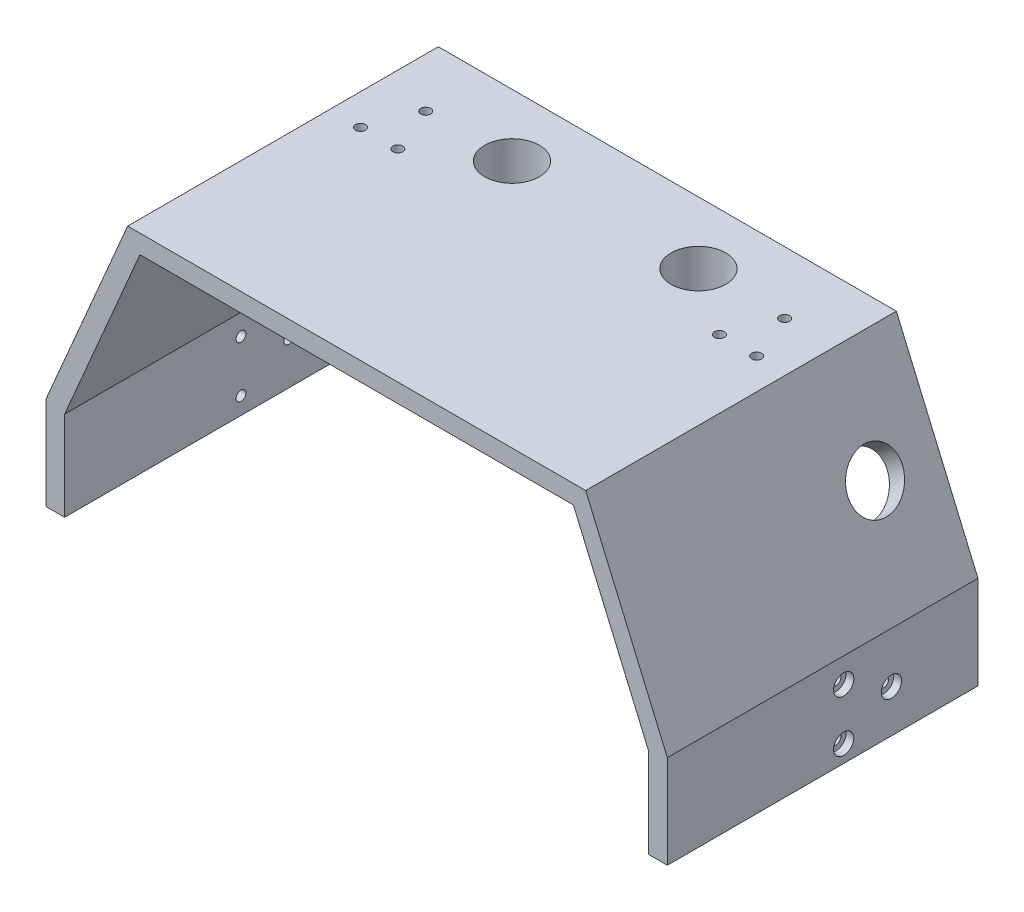
SolidWorks part; units mm, degrees
ref_plane "Alzado" through (0, 0, 0) normal (0, 0, 1) x (1, 0, 0)
ref_plane "Planta" through (0, 0, 0) normal (0, 1, 0) x (1, 0, 0)
ref_plane "Vista lateral" through (0, 0, 0) normal (1, 0, 0) x (0, 0, -1)
sketch "Croquis1" plane through (0, 0, 0) normal (0, 0, 1) x (1, 0, 0)
  line L1 (-100, 25) -> (-73.7179, 86.3249) construction
  line L2 (-73.7179, 86.3249) -> (73.7179, 86.3249) construction
  line L3 (100, 25) -> (100, -5) construction
  line L4 (100, 25) -> (73.7179, 86.3249) construction
  line L5 (-100, 25) -> (-100, -5)
  line L6 (-100, 25) -> (-73.7179, 86.3249)
  line L7 (-73.7179, 86.3249) -> (73.7179, 86.3249)
  line L8 (100, 25) -> (100, -5)
  line L9 (100, 25) -> (73.7179, 86.3249)
  line L10 (-94, 23.7685) -> (-94, -5)
  line L11 (-94, 23.7685) -> (-69.7615, 80.3249)
  line L12 (-69.7615, 80.3249) -> (69.7615, 80.3249)
  line L13 (94, 23.7685) -> (69.7615, 80.3249)
  line L14 (94, 23.7685) -> (94, -5)
  line L15 (-94, -5) -> (-100, -5)
  line L16 (100, -5) -> (94, -5)
  dimension "D2" = 30
  dimension "D1" = 6
extrude "Saliente-Extruir1" add sketch "Croquis1" along normal blind 100
sketch "Croquis3" plane through (0, 86.3249, 0) normal (0, 1, 0) x (1, 0, 0)
  line L0 (73.7179, 0) -> (-73.7179, 0) construction
  line L1 (73.7179, -100) -> (73.7179, 0) construction
  line L2 (-73.7179, -100) -> (-73.7179, 0) construction
  circle A2 centre (-30, -20) radius 8.8
  circle A3 centre (30, -20) radius 8.8
  dimension "D4" = 17.6
  dimension "D5" = 17.6
  dimension "D1" = 20
  dimension "D2" = 20
  dimension "D3" = 43.7179
  dimension "D6" = 43.7179
extrude "Cortar-Extruir1" cut sketch "Croquis3" against normal up to next
ref_plane "Plano1" through (-87.4795, 68.8361, 0) normal (-0.7859, 0.6184, 0) x (0, 0, -1)
sketch "Croquis4" plane through (-87.4795, 68.8361, 0) normal (-0.7859, 0.6184, 0) x (0, 0, -1)
  line L0 (0, -22.254) -> (0, 42.1921) construction
  line L1 (-100, -22.254) -> (0, -22.254) construction
  line L2 (-100, -22.254) -> (-100, 42.1921) construction
  line L3 (-100, 42.1921) -> (0, 42.1921) construction
  line L4 (0, -22.254) -> (0, 42.1921) construction
  line L5 (-100, -22.254) -> (0, -22.254) construction
  line L6 (-100, -22.254) -> (-100, 42.1921) construction
  line L7 (-100, 42.1921) -> (0, 42.1921) construction
  line L8 (0, 9.9691) -> (-100, 9.9691) construction
  circle A0 centre (-20, 9.9691) radius 8.8
  dimension "D1" = 17.6
  dimension "D2" = 20
extrude "Cortar-Extruir2" cut sketch "Croquis4" against normal up to next
mirror "Simetría1" about plane through (0, 0, 0) normal (1, 0, 0) of "Cortar-Extruir2"
sketch "Croquis5" plane through (0, 80.3249, 0) normal (0, -1, 0) x (1, 0, 0)
  line L0 (15.175, 0) -> (15.175, 2.3)
  line L1 (15.175, 2.3) -> (3.7842, 2.3)
  line L3 (-3.7842, 2.3) -> (-15.175, 2.3)
  line L4 (-15.175, 2.3) -> (-15.175, 0)
  line L10 (-14.875, 0) -> (-3.2619, 0)
  line L11 (3.2619, 0) -> (14.875, 0)
  line L12 (14.875, 0) -> (14.875, 2)
  line L13 (14.875, 2) -> (3.7202, 2)
  line L14 (-3.7202, 2) -> (-14.875, 2)
  line L15 (-14.875, 2) -> (-14.875, 0)
  line L17 (-15.175, 0) -> (3.2619, 0)
  line L19 (-3.2619, 0) -> (15.175, 0)
  line L20 (14.875, 0) -> (14.875, 2)
  line L22 (14.875, 2) -> (3.7202, 2)
  line L23 (-3.7202, 2) -> (-14.875, 2)
  line L24 (-14.875, 2) -> (-14.875, 0)
  arc A0 (3.7842, 2.3) -> (-3.7842, 2.3) centre (0, -6.25) ccw
  arc A3 (3.2619, 0) -> (-3.2619, 0) centre (0, -6.25) ccw
  arc A4 (3.7202, 2) -> (-3.7202, 2) centre (0, -6.25) ccw
  arc A5 (3.2619, 0) -> (-3.2619, 0) centre (0, -6.25) ccw
  arc A7 (3.7202, 2) -> (-3.7202, 2) centre (0, -6.25) ccw
  dimension "D1" = 0
  dimension "D2" = 0.3
extrude "Cortar-Extruir3" cut sketch "Croquis5" against normal blind 0.5
sketch "Croquis6" plane through (-100, 0, 0) normal (-1, 0, 0) x (0, 0, 1)
  circle A0 centre (43.227, 0.4977) radius 1.6 construction
  circle A1 centre (27.8635, 8.7685) radius 1.6 construction
  circle A2 centre (43.227, 17.0392) radius 1.6 construction
  circle A3 centre (43.227, 0.4977) radius 1.6
  circle A4 centre (27.8635, 8.7685) radius 1.6
  circle A5 centre (43.227, 17.0392) radius 1.6
extrude "Cortar-Extruir4" cut sketch "Croquis6" against normal up to next
sketch "Croquis7" plane through (-100, 0, 0) normal (-1, 0, 0) x (0, 0, 1)
  circle A0 centre (27.8635, 8.7685) radius 3.25
  circle A1 centre (43.227, 0.4977) radius 3.25
  circle A2 centre (43.227, 17.0392) radius 3.25
  dimension "D1" = 6.5
extrude "Cortar-Extruir5" cut sketch "Croquis7" against normal blind 2.5
mirror "Simetría2" about plane through (0, 0, 0) normal (1, 0, 0) of "Cortar-Extruir5", "Cortar-Extruir4"
sketch "Croquis11" plane through (0, 80.3249, 0) normal (0, -1, 0) x (1, 0, 0)
  circle A0 centre (30, 20) radius 8.8 construction
  circle A1 centre (-30, 20) radius 8.8 construction
  circle A2 centre (30, 20) radius 8.8
  circle A3 centre (-30, 20) radius 8.8
  circle A4 centre (-30, 20) radius 10.3
  circle A5 centre (30, 20) radius 10.3
  dimension "D1" = 1.5
extrude "Saliente-Extruir2" add sketch "Croquis11" along normal blind 10
ref_plane "Plano2" through (-63.9034, 50.2844, 0) normal (-0.7859, 0.6184, 0) x (0, 0, -1)
sketch "Croquis12" plane through (-63.9034, 50.2844, 0) normal (-0.7859, 0.6184, 0) x (0, 0, -1)
  circle A0 centre (-20, 9.9691) radius 8.8 construction
  circle A1 centre (-20, 9.9691) radius 8.8
  circle A2 centre (-20, 9.9691) radius 10.3
  dimension "D1" = 1.5
extrude "Saliente-Extruir3" add sketch "Croquis12" along normal up to next
sketch "Croquis13" plane through (0, 80.3249, 0) normal (0, -1, 0) x (1, 0, 0)
  circle A0 centre (57.7615, 20) radius 1.6 construction
  circle A1 centre (51.7615, 35) radius 1.6 construction
  circle A2 centre (63.7615, 35) radius 1.6 construction
  circle A3 centre (-57.7615, 20) radius 1.6 construction
  circle A4 centre (-63.7615, 35) radius 1.6 construction
  circle A5 centre (-51.7615, 35) radius 1.6 construction
  circle A6 centre (57.7615, 20) radius 1.6
  circle A7 centre (51.7615, 35) radius 1.6
  circle A8 centre (63.7615, 35) radius 1.6
  circle A9 centre (-57.7615, 20) radius 1.6
  circle A10 centre (-63.7615, 35) radius 1.6
  circle A11 centre (-51.7615, 35) radius 1.6
extrude "Cortar-Extruir9" cut sketch "Croquis13" against normal up to next
